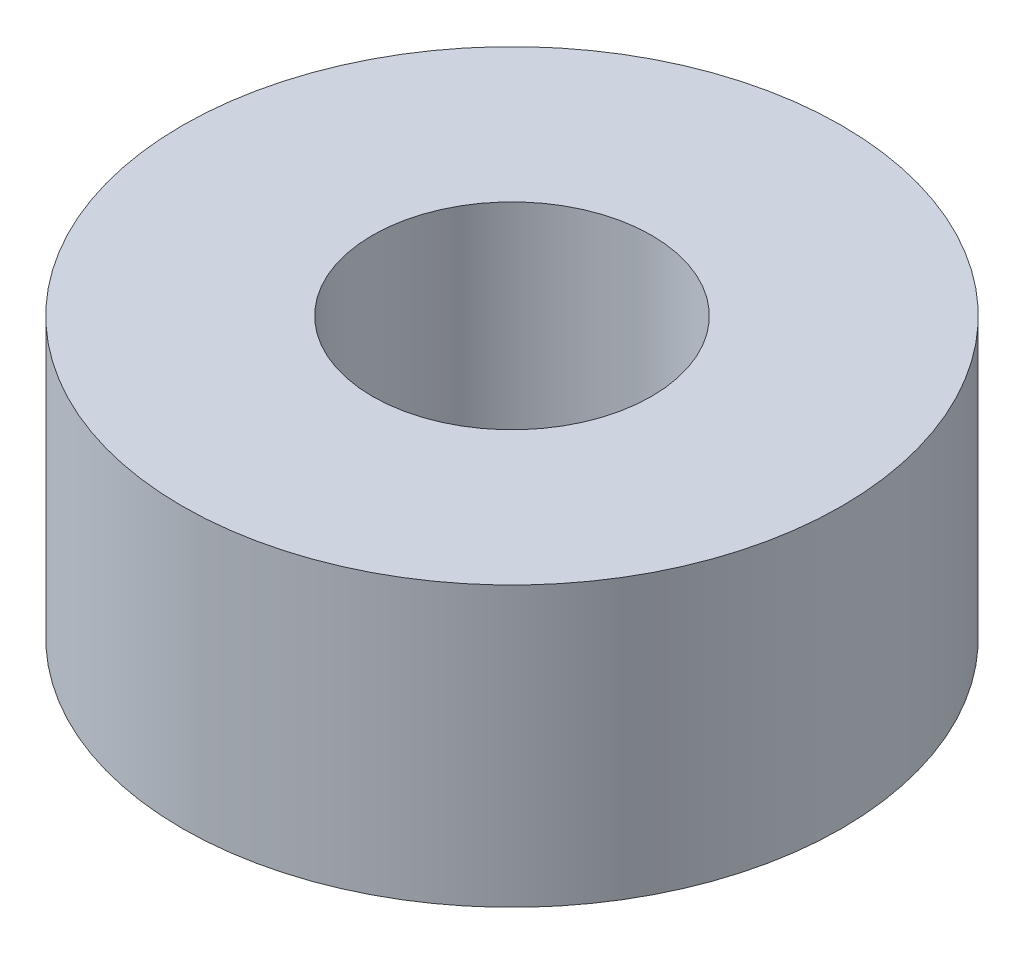
SolidWorks part; units mm, degrees
ref_plane "Front Plane" through (0, 0, 0) normal (0, 0, 1) x (1, 0, 0)
ref_plane "Top Plane" through (0, 0, 0) normal (0, 1, 0) x (1, 0, 0)
ref_plane "Right Plane" through (0, 0, 0) normal (1, 0, 0) x (0, 0, -1)
sketch "Sketch1" plane through (0, 0, 0) normal (0, 1, 0) x (1, 0, 0)
  circle A0 centre (0, 0) radius 7.5
  circle A1 centre (0, 0) radius 3.175
  dimension "D1" = 15
  dimension "D2" = 6.35
extrude "Boss-Extrude1" add sketch "Sketch1" along normal blind 6.35
